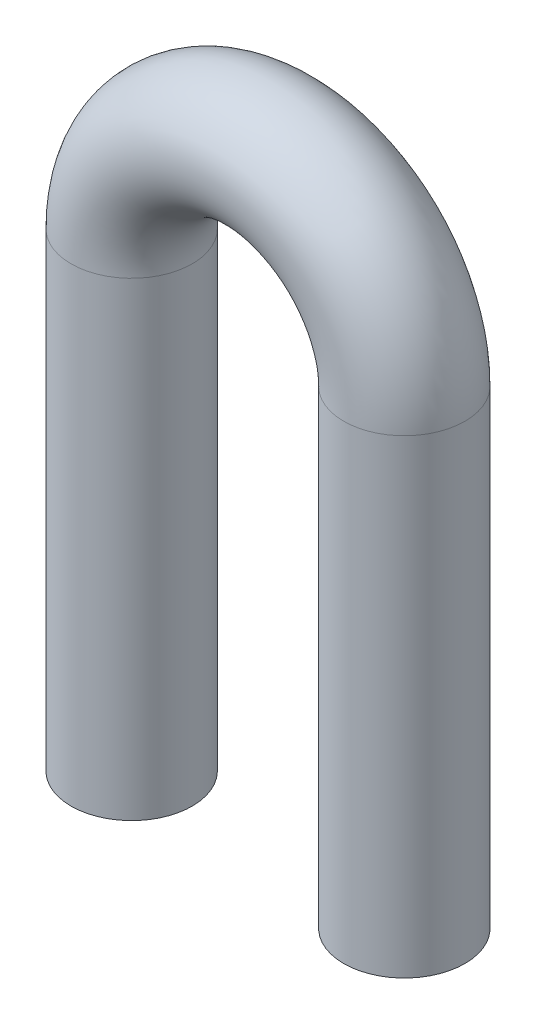
SolidWorks part; units mm, degrees
ref_plane "Plano frontal" through (0, 0, 0) normal (0, 0, 1) x (1, 0, 0)
ref_plane "Plano superior" through (0, 0, 0) normal (0, 1, 0) x (1, 0, 0)
ref_plane "Plano direito" through (0, 0, 0) normal (1, 0, 0) x (0, 0, -1)
sketch "Sketch1" plane through (0, 0, 0) normal (0, 0, 1) x (1, 0, 0)
  line L0 (0, 0) -> (0, 15.5)
  line L2 (9, 15.5) -> (9, 0)
  arc A0 (0, 15.5) -> (9, 15.5) centre (4.5, 15.5) cw
  point P9 (4.5, 20)
  dimension "D1" = 9
  dimension "D2" = 20
sketch "Sketch2" plane through (0, 0, 0) normal (0, 1, 0) x (1, 0, 0)
  circle A0 centre (0, 0) radius 2
  dimension "D1" = 4
sweep "Sweep1" add profiles "Sketch2" path "Sketch1"
